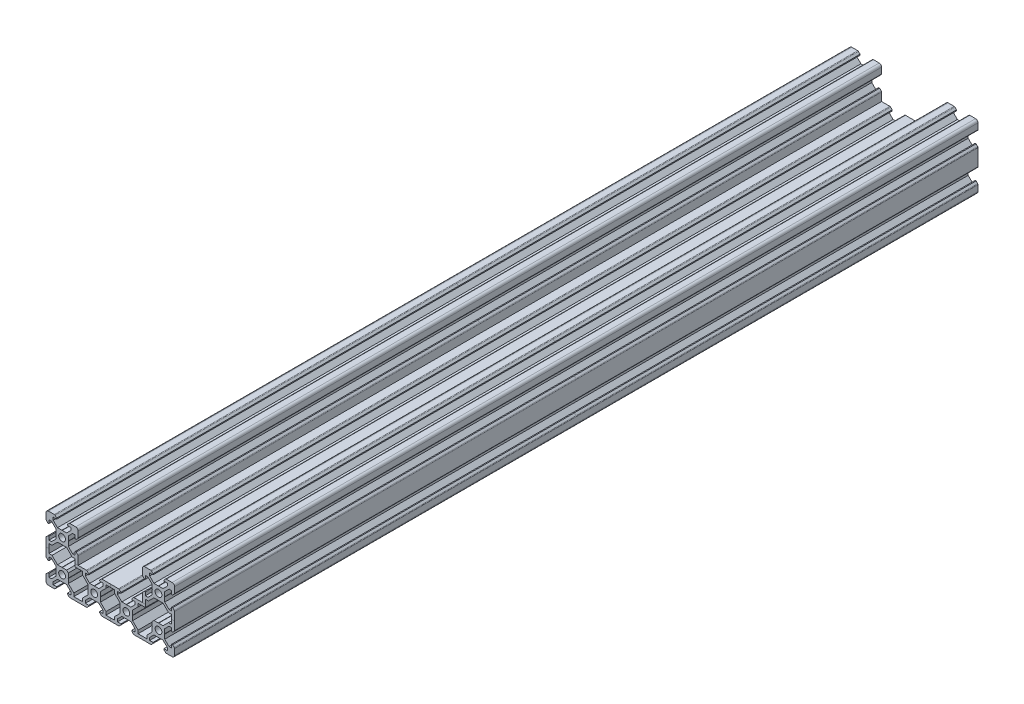
SolidWorks part; units mm, degrees
material "6063-T5"
ref_plane "Front" through (0, 0, 0) normal (0, 0, 1) x (1, 0, 0)
ref_plane "Top" through (0, 0, 0) normal (0, 1, 0) x (1, 0, 0)
ref_plane "Right" through (0, 0, 0) normal (1, 0, 0) x (0, 0, -1)
sketch "Sketch1" plane through (0, 0, 0) normal (0, 0, 1) x (1, 0, 0)
  line L0 (0, 32.3219) -> (0, -50.1713) construction
  line L1 (-2.8395, 3.9) -> (-0.1, 3.9)
  line L2 (-3.9, 2.8395) -> (-3.9, 0.1)
  line L3 (-2.8395, -3.9) -> (-0.1, -3.9)
  line L4 (3.9, 2.8395) -> (3.9, 0.1)
  line L5 (-29.7903, 0) -> (30, 0) construction
  line L6 (-0.1, -3.9) -> (0, -3.8)
  line L7 (-8.5, 10) -> (-4.8658, 10)
  line L8 (-10, 8.5) -> (-10, 4.8627)
  line L9 (-2.8395, -16.1) -> (-6.24, -12.6995)
  line L10 (10, 8.5) -> (10, 4.8627)
  line L11 (0, -3.8) -> (0.1, -3.9)
  line L12 (0.1, -3.9) -> (2.8395, -3.9)
  line L13 (-0.1, 3.9) -> (0, 3.8)
  line L14 (0, 3.8) -> (0.1, 3.9)
  line L15 (10, -10) -> (-10, 10) construction
  line L16 (-10, -10) -> (10, 10) construction
  line L17 (0.1, 3.9) -> (2.8395, 3.9)
  line L18 (-3.9, 0.1) -> (-3.8, 0)
  line L19 (-3.8, 0) -> (-3.9, -0.1)
  line L20 (-3.9, -0.1) -> (-3.9, -2.8395)
  line L21 (3.9, 0.1) -> (3.8, 0)
  line L22 (3.8, 0) -> (3.9, -0.1)
  line L23 (3.9, -0.1) -> (3.9, -2.8395)
  line L24 (0, -20) -> (58.4732, -20) construction
  line L25 (-3.9, 2.8395) -> (-6.561, 5.5005)
  line L26 (30, -50.1713) -> (30, 32.3219) construction
  line L27 (-5.5005, 8.2) -> (-3.3865, 8.2)
  line L28 (-8.2, 5.5005) -> (-8.2, 3.3865)
  line L29 (-10, -10) -> (-53.8942, -10) construction
  line L30 (8.2, 5.5005) -> (8.2, 3.3865)
  line L31 (-6.561, 5.5005) -> (-8.2, 5.5005)
  line L32 (-2.8395, 3.9) -> (-5.5005, 6.561)
  line L33 (-5.5005, 6.561) -> (-5.5005, 8.2)
  line L34 (6.561, 5.5005) -> (8.2, 5.5005)
  line L35 (3.9, 2.8395) -> (6.561, 5.5005)
  line L36 (5.5005, 6.561) -> (5.5005, 8.2)
  line L37 (2.8395, 3.9) -> (5.5005, 6.561)
  line L38 (6.561, -5.5005) -> (8.2, -5.5005)
  line L39 (-8.2, -12.6995) -> (-8.2, -7.3005)
  line L40 (2.8395, -3.9) -> (5.5005, -6.561)
  line L41 (3.9, -2.8395) -> (6.561, -5.5005)
  line L42 (-6.24, -12.6995) -> (-8.2, -12.6995)
  line L43 (-2.8395, -3.9) -> (-5.5005, -6.561)
  line L44 (-6.561, -5.5005) -> (-8.2, -5.5005)
  line L45 (-3.9, -2.8395) -> (-6.561, -5.5005)
  line L46 (30, -10) -> (10, -10) construction
  line L47 (-8.5, 10) -> (-10, 8.5) construction
  line L48 (8.5, 10) -> (10, 8.5) construction
  line L49 (-10, -10) -> (10, -30) construction
  line L50 (-5.5005, -6.561) -> (-6.24, -7.3005)
  line L51 (-3.9, -19.9) -> (-3.9, -17.1605)
  line L52 (-3.9, -17.1605) -> (-6.561, -14.4995)
  line L53 (10, 32.3219) -> (10, -50.1713) construction
  line L54 (-10, -30) -> (10, -10) construction
  line L55 (-4.3771, 9.7976) -> (-3.3865, 8.807)
  line L56 (-3.3865, 8.807) -> (-3.3865, 8.2)
  line L57 (4.3771, 9.7976) -> (3.3865, 8.807)
  line L58 (3.3865, 8.807) -> (3.3865, 8.2)
  line L59 (4.8658, 10) -> (8.5, 10)
  line L60 (3.3865, 8.2) -> (5.5005, 8.2)
  line L61 (-9.7968, 4.3732) -> (-8.807, 3.3865)
  line L62 (-8.807, 3.3865) -> (-8.2, 3.3865)
  line L63 (-9.7976, -4.3802) -> (-8.807, -3.3865)
  line L64 (-8.807, -3.3865) -> (-8.2, -3.3865)
  line L65 (9.7968, 4.3732) -> (8.807, 3.3865)
  line L66 (8.807, 3.3865) -> (8.2, 3.3865)
  line L67 (8.807, -3.3865) -> (8.2, -3.3865)
  line L68 (9.7976, -4.3802) -> (8.807, -3.3865)
  line L69 (-10, -4.87) -> (-10, -15.13)
  line L70 (-8.2, -3.3865) -> (-8.2, -5.5005)
  line L71 (10, -4.87) -> (10, -10)
  line L72 (8.2, -3.3865) -> (8.2, -5.5005)
  line L73 (-6.561, -14.4995) -> (-8.2, -14.4995)
  line L74 (-8.2, -16.6135) -> (-8.2, -14.4995)
  line L75 (-8.807, -16.6135) -> (-8.2, -16.6135)
  line L76 (-9.7976, -15.6198) -> (-8.807, -16.6135)
  line L77 (-10, -28.5) -> (-10, -24.8627)
  line L78 (-9.7968, -24.3732) -> (-8.807, -23.3865)
  line L79 (-8.807, -23.3865) -> (-8.2, -23.3865)
  line L80 (-8.2, -25.5005) -> (-8.2, -23.3865)
  line L81 (-6.561, -25.5005) -> (-8.2, -25.5005)
  line L82 (-3.9, -22.8395) -> (-6.561, -25.5005)
  line L83 (-3.9, -22.8395) -> (-3.9, -20.1)
  line L84 (-3.9, -20.1) -> (-3.8, -20)
  line L85 (-3.8, -20) -> (-3.9, -19.9)
  line L86 (0, -23.8) -> (0.1, -23.9)
  line L87 (-0.1, -23.9) -> (0, -23.8)
  line L88 (-2.8395, -23.9) -> (-0.1, -23.9)
  line L89 (0.1, -23.9) -> (2.8395, -23.9)
  line L90 (-2.8395, -23.9) -> (-5.5005, -26.561)
  line L91 (-5.5005, -28.2) -> (-3.3865, -28.2)
  line L92 (-5.5005, -26.561) -> (-5.5005, -28.2)
  line L93 (-4.3771, -29.7976) -> (-3.3865, -28.807)
  line L94 (-3.3865, -28.807) -> (-3.3865, -28.2)
  line L95 (-4.8658, -30) -> (-8.5, -30)
  line L96 (5.5005, -26.561) -> (5.5005, -28.2)
  line L97 (2.8395, -23.9) -> (5.5005, -26.561)
  line L98 (4.3771, -29.7976) -> (3.3865, -28.807)
  line L99 (3.3865, -28.807) -> (3.3865, -28.2)
  line L100 (3.3865, -28.2) -> (5.5005, -28.2)
  line L101 (4.8658, -30) -> (10, -30)
  line L102 (0.1, -16.1) -> (2.8395, -16.1)
  line L103 (0, -16.2) -> (0.1, -16.1)
  line L104 (-0.1, -16.1) -> (0, -16.2)
  line L105 (-2.8395, -16.1) -> (-0.1, -16.1)
  line L106 (3.9, -22.8395) -> (3.9, -20.1)
  line L107 (3.9, -20.1) -> (3.8, -20)
  line L108 (3.8, -20) -> (3.9, -19.9)
  line L109 (3.9, -19.9) -> (3.9, -17.1605)
  line L110 (3.9, -17.1605) -> (2.8395, -16.1)
  line L111 (-6.24, -7.3005) -> (-8.2, -7.3005)
  line L112 (6.24, -7.3005) -> (8.2, -7.3005)
  line L113 (5.5005, -6.561) -> (6.24, -7.3005)
  line L114 (12.6995, -28.2) -> (7.3005, -28.2)
  line L115 (7.3005, -28.2) -> (7.3005, -26.24)
  line L116 (7.3005, -26.24) -> (3.9, -22.8395)
  line L117 (16.1, -19.9) -> (16.1, -17.1605)
  line L118 (16.2, -20) -> (16.1, -19.9)
  line L119 (16.1, -20.1) -> (16.2, -20)
  line L120 (16.1, -22.8395) -> (16.1, -20.1)
  line L121 (20, -16.2) -> (19.9, -16.1)
  line L122 (20.1, -16.1) -> (20, -16.2)
  line L123 (22.8395, -16.1) -> (20.1, -16.1)
  line L124 (19.9, -16.1) -> (17.1605, -16.1)
  line L125 (23.9, -19.9) -> (23.9, -17.1605)
  line L126 (23.8, -20) -> (23.9, -19.9)
  line L127 (23.9, -20.1) -> (23.8, -20)
  line L128 (23.9, -22.8395) -> (23.9, -20.1)
  line L129 (20.1, -23.9) -> (20, -23.8)
  line L130 (22.8395, -23.9) -> (20.1, -23.9)
  line L131 (20, -23.8) -> (19.9, -23.9)
  line L132 (19.9, -23.9) -> (17.1605, -23.9)
  line L133 (12.6995, -28.2) -> (12.6995, -26.24)
  line L134 (14.4995, -26.561) -> (14.4995, -28.2)
  line L135 (17.1605, -23.9) -> (14.4995, -26.561)
  line L136 (12.6995, -26.24) -> (16.1, -22.8395)
  line L137 (16.6135, -28.807) -> (16.6135, -28.2)
  line L138 (16.6135, -28.2) -> (14.4995, -28.2)
  line L139 (15.6229, -29.7976) -> (16.6135, -28.807)
  line L140 (15.1342, -30) -> (10, -30)
  line L141 (20, 32.3219) -> (20, -50.1713) construction
  line L142 (10, -10) -> (30, -30) construction
  line L143 (30, -10) -> (10, -30) construction
  line L144 (27.3005, -28.2) -> (27.3005, -26.24)
  line L145 (25.5005, -26.561) -> (25.5005, -28.2)
  line L146 (24.3771, -29.7976) -> (23.3865, -28.807)
  line L147 (23.3865, -28.807) -> (23.3865, -28.2)
  line L148 (23.3865, -28.2) -> (25.5005, -28.2)
  line L149 (24.8658, -30) -> (30, -30)
  line L150 (27.3005, -28.2) -> (32.6995, -28.2)
  line L151 (25.5005, -26.561) -> (22.8395, -23.9)
  line L152 (27.3005, -26.24) -> (23.9, -22.8395)
  line L153 (25.5005, -13.439) -> (25.5005, -11.8)
  line L154 (27.3005, -11.8) -> (27.3005, -13.76)
  line L155 (27.3005, -13.76) -> (23.9, -17.1605)
  line L156 (25.5005, -13.439) -> (22.8395, -16.1)
  line L157 (12.6995, -11.8) -> (12.6995, -13.76)
  line L158 (14.4995, -13.439) -> (14.4995, -11.8)
  line L159 (17.1605, -16.1) -> (14.4995, -13.439)
  line L160 (16.1, -17.1605) -> (12.6995, -13.76)
  line L161 (23.3865, -11.193) -> (23.3865, -11.8)
  line L162 (16.6135, -11.193) -> (16.6135, -11.8)
  line L163 (16.6135, -11.8) -> (14.4995, -11.8)
  line L164 (23.3865, -11.8) -> (25.5005, -11.8)
  line L165 (15.6229, -10.2024) -> (16.6135, -11.193)
  line L166 (24.3771, -10.2024) -> (23.3865, -11.193)
  line L167 (24.8658, -10) -> (30, -10)
  line L168 (27.3005, -11.8) -> (32.6995, -11.8)
  line L169 (15.1342, -10) -> (10, -10)
  line L170 (12.6995, -11.8) -> (8.2, -11.8)
  line L171 (8.2, -11.8) -> (8.2, -7.3005)
  line L172 (60, -3.8) -> (59.9, -3.9)
  line L173 (60.1, -3.9) -> (60, -3.8)
  line L174 (63.8, 0) -> (63.9, -0.1)
  line L175 (63.9, 0.1) -> (63.8, 0)
  line L176 (56.1, 0.1) -> (56.2, 0)
  line L177 (56.2, 0) -> (56.1, -0.1)
  line L178 (60.1, 3.9) -> (60, 3.8)
  line L179 (60, 3.8) -> (59.9, 3.9)
  line L180 (62.8395, 3.9) -> (60.1, 3.9)
  line L181 (59.9, 3.9) -> (57.1605, 3.9)
  line L182 (63.9, 2.8395) -> (63.9, 0.1)
  line L183 (63.9, -0.1) -> (63.9, -2.8395)
  line L184 (62.8395, -3.9) -> (60.1, -3.9)
  line L185 (59.9, -3.9) -> (57.1605, -3.9)
  line L186 (56.1, -0.1) -> (56.1, -2.8395)
  line L187 (56.1, 2.8395) -> (56.1, 0.1)
  line L188 (60, -23.8) -> (59.9, -23.9)
  line L189 (60.1, -23.9) -> (60, -23.8)
  line L190 (60, -16.2) -> (59.9, -16.1)
  line L191 (60.1, -16.1) -> (60, -16.2)
  line L192 (63.8, -20) -> (63.9, -19.9)
  line L193 (63.9, -20.1) -> (63.8, -20)
  line L194 (56.2, -20) -> (56.1, -19.9)
  line L195 (56.1, -20.1) -> (56.2, -20)
  line L196 (40, -16.2) -> (40.1, -16.1)
  line L197 (39.9, -16.1) -> (40, -16.2)
  line L198 (36.2, -20) -> (36.1, -19.9)
  line L199 (36.1, -20.1) -> (36.2, -20)
  line L200 (43.8, -20) -> (43.9, -19.9)
  line L201 (43.9, -20.1) -> (43.8, -20)
  line L202 (40, -23.8) -> (40.1, -23.9)
  line L203 (39.9, -23.9) -> (40, -23.8)
  line L204 (56.1, -22.8395) -> (56.1, -20.1)
  line L205 (59.9, -23.9) -> (57.1605, -23.9)
  line L206 (62.8395, -23.9) -> (60.1, -23.9)
  line L207 (63.9, -22.8395) -> (63.9, -20.1)
  line L208 (63.9, -19.9) -> (63.9, -17.1605)
  line L209 (62.8395, -16.1) -> (60.1, -16.1)
  line L210 (59.9, -16.1) -> (57.1605, -16.1)
  line L211 (56.1, -19.9) -> (56.1, -17.1605)
  line L212 (43.9, -19.9) -> (43.9, -17.1605)
  line L213 (43.9, -22.8395) -> (43.9, -20.1)
  line L214 (40.1, -23.9) -> (42.8395, -23.9)
  line L215 (37.1605, -23.9) -> (39.9, -23.9)
  line L216 (36.1, -22.8395) -> (36.1, -20.1)
  line L217 (36.1, -19.9) -> (36.1, -17.1605)
  line L218 (37.1605, -16.1) -> (39.9, -16.1)
  line L219 (40.1, -16.1) -> (42.8395, -16.1)
  line L220 (42.8395, -23.9) -> (45.5005, -26.561)
  line L221 (47.3005, -26.24) -> (43.9, -22.8395)
  line L222 (43.9, -17.1605) -> (47.3005, -13.76)
  line L223 (42.8395, -16.1) -> (45.5005, -13.439)
  line L224 (34.4995, -13.439) -> (37.1605, -16.1)
  line L225 (32.6995, -13.76) -> (36.1, -17.1605)
  line L226 (34.4995, -26.561) -> (37.1605, -23.9)
  line L227 (32.6995, -26.24) -> (36.1, -22.8395)
  line L228 (47.3005, -11.8) -> (47.3005, -13.76)
  line L229 (45.5005, -13.439) -> (45.5005, -11.8)
  line L230 (47.3005, -28.2) -> (47.3005, -26.24)
  line L231 (45.5005, -26.561) -> (45.5005, -28.2)
  line L232 (34.4995, -26.561) -> (34.4995, -28.2)
  line L233 (32.6995, -28.2) -> (32.6995, -26.24)
  line L234 (34.4995, -13.439) -> (34.4995, -11.8)
  line L235 (32.6995, -11.8) -> (32.6995, -13.76)
  line L236 (43.3865, -28.2) -> (45.5005, -28.2)
  line L237 (43.3865, -28.807) -> (43.3865, -28.2)
  line L238 (44.3771, -29.7976) -> (43.3865, -28.807)
  line L239 (35.6229, -29.7976) -> (36.6135, -28.807)
  line L240 (36.6135, -28.807) -> (36.6135, -28.2)
  line L241 (36.6135, -28.2) -> (34.4995, -28.2)
  line L242 (44.3771, -10.2024) -> (43.3865, -11.193)
  line L243 (43.3865, -11.193) -> (43.3865, -11.8)
  line L244 (43.3865, -11.8) -> (45.5005, -11.8)
  line L245 (35.6229, -10.2024) -> (36.6135, -11.193)
  line L246 (36.6135, -11.193) -> (36.6135, -11.8)
  line L247 (36.6135, -11.8) -> (34.4995, -11.8)
  line L248 (35.1342, -30) -> (30, -30)
  line L249 (35.1342, -10) -> (30, -10)
  line L250 (51.8, -3.3865) -> (51.8, -5.5005)
  line L251 (51.193, -3.3865) -> (51.8, -3.3865)
  line L252 (50.2024, -4.3802) -> (51.193, -3.3865)
  line L253 (51.8, -11.8) -> (51.8, -7.3005)
  line L254 (50, -4.87) -> (50, -10)
  line L255 (44.8658, -10) -> (50, -10)
  line L256 (47.3005, -11.8) -> (51.8, -11.8)
  line L257 (62.8395, -16.1) -> (66.24, -12.6995)
  line L258 (63.9, -17.1605) -> (66.561, -14.4995)
  line L259 (63.9, -22.8395) -> (66.561, -25.5005)
  line L260 (62.8395, -23.9) -> (65.5005, -26.561)
  line L261 (57.1605, -23.9) -> (54.4995, -26.561)
  line L262 (52.6995, -26.24) -> (56.1, -22.8395)
  line L263 (63.9, 2.8395) -> (66.561, 5.5005)
  line L264 (62.8395, 3.9) -> (65.5005, 6.561)
  line L265 (57.1605, 3.9) -> (54.4995, 6.561)
  line L266 (56.1, 2.8395) -> (53.439, 5.5005)
  line L267 (63.9, -2.8395) -> (66.561, -5.5005)
  line L268 (62.8395, -3.9) -> (65.5005, -6.561)
  line L269 (57.1605, -3.9) -> (54.4995, -6.561)
  line L270 (56.1, -2.8395) -> (53.439, -5.5005)
  line L271 (64.3771, -29.7976) -> (63.3865, -28.807)
  line L272 (64.8658, -30) -> (68.5, -30)
  line L273 (65.5005, -28.2) -> (63.3865, -28.2)
  line L274 (55.6229, -29.7976) -> (56.6135, -28.807)
  line L275 (56.6135, -28.2) -> (54.4995, -28.2)
  line L276 (56.6135, -28.807) -> (56.6135, -28.2)
  line L277 (55.1342, -30) -> (50, -30)
  line L278 (44.8658, -30) -> (50, -30)
  line L279 (44.3771, -29.7976) -> (43.3865, -28.807)
  line L280 (43.3865, -28.807) -> (43.3865, -28.2)
  line L281 (43.3865, -28.2) -> (45.5005, -28.2)
  line L282 (47.3005, -28.2) -> (52.6995, -28.2)
  line L283 (70, -28.5) -> (70, -24.8627)
  line L284 (65.5005, -26.561) -> (65.5005, -28.2)
  line L285 (54.4995, -26.561) -> (54.4995, -28.2)
  line L286 (52.6995, -28.2) -> (52.6995, -26.24)
  line L287 (47.3005, -28.2) -> (47.3005, -26.24)
  line L288 (45.5005, -26.561) -> (45.5005, -28.2)
  line L289 (66.561, -5.5005) -> (68.2, -5.5005)
  line L290 (66.24, -7.3005) -> (68.2, -7.3005)
  line L291 (69.7976, -4.3802) -> (68.807, -3.3865)
  line L292 (68.807, -3.3865) -> (68.2, -3.3865)
  line L293 (68.2, -3.3865) -> (68.2, -5.5005)
  line L294 (68.2, -12.6995) -> (68.2, -7.3005)
  line L295 (70, -4.87) -> (70, -15.13)
  line L296 (69.7976, -15.6198) -> (68.807, -16.6135)
  line L297 (68.807, -16.6135) -> (68.2, -16.6135)
  line L298 (68.2, -16.6135) -> (68.2, -14.4995)
  line L299 (66.561, -14.4995) -> (68.2, -14.4995)
  line L300 (66.24, -12.6995) -> (68.2, -12.6995)
  line L301 (56.1, -17.1605) -> (57.1605, -16.1)
  line L302 (66.561, -25.5005) -> (68.2, -25.5005)
  line L303 (68.2, -25.5005) -> (68.2, -23.3865)
  line L304 (68.807, -23.3865) -> (68.2, -23.3865)
  line L305 (69.7968, -24.3732) -> (68.807, -23.3865)
  line L306 (53.76, -7.3005) -> (51.8, -7.3005)
  line L307 (53.439, -5.5005) -> (51.8, -5.5005)
  line L308 (54.4995, -6.561) -> (53.76, -7.3005)
  line L309 (65.5005, -6.561) -> (66.24, -7.3005)
  line L310 (54.4995, 6.561) -> (54.4995, 8.2)
  line L311 (56.6135, 8.2) -> (54.4995, 8.2)
  line L312 (56.6135, 8.807) -> (56.6135, 8.2)
  line L313 (55.6229, 9.7976) -> (56.6135, 8.807)
  line L314 (55.1342, 10) -> (51.5, 10)
  line L315 (50, 8.5) -> (50, 4.8627)
  line L316 (50.2032, 4.3732) -> (51.193, 3.3865)
  line L317 (51.193, 3.3865) -> (51.8, 3.3865)
  line L318 (51.8, 5.5005) -> (51.8, 3.3865)
  line L319 (53.439, 5.5005) -> (51.8, 5.5005)
  line L320 (66.561, 5.5005) -> (68.2, 5.5005)
  line L321 (68.2, 5.5005) -> (68.2, 3.3865)
  line L322 (68.807, 3.3865) -> (68.2, 3.3865)
  line L323 (69.7968, 4.3732) -> (68.807, 3.3865)
  line L324 (70, 8.5) -> (70, 4.8627)
  line L325 (68.5, 10) -> (64.8658, 10)
  line L326 (64.3771, 9.7976) -> (63.3865, 8.807)
  line L327 (63.3865, 8.807) -> (63.3865, 8.2)
  line L328 (65.5005, 8.2) -> (63.3865, 8.2)
  line L329 (65.5005, 6.561) -> (65.5005, 8.2)
  line L330 (63.3865, -28.807) -> (63.3865, -28.2)
  circle A0 centre (0, 0) radius 2.1
  circle A1 centre (0, -20) radius 2.1
  circle A2 centre (20, -20) radius 2.1
  circle A3 centre (60, 0) radius 2.1
  circle A4 centre (60, -20) radius 2.1
  circle A5 centre (40, -20) radius 2.1
  arc A6 (-8.5, 10) -> (-10, 8.5) centre (-8.5, 8.5) ccw
  arc A7 (10, 8.5) -> (8.5, 10) centre (8.5, 8.5) ccw
  arc A8 (-4.3771, 9.7976) -> (-4.8658, 10) centre (-4.8658, 9.3088) ccw
  arc A9 (4.3771, 9.7976) -> (4.8658, 10) centre (4.8658, 9.3088) cw
  arc A10 (-10, 4.8627) -> (-9.7968, 4.3732) centre (-9.3088, 4.8627) ccw
  arc A11 (9.7968, 4.3732) -> (10, 4.8627) centre (9.3088, 4.8627) ccw
  arc A12 (10, -4.87) -> (9.7976, -4.3802) centre (9.3062, -4.87) ccw
  arc A13 (-9.7976, -4.3802) -> (-10, -4.87) centre (-9.3062, -4.87) ccw
  arc A14 (-9.7976, -15.6198) -> (-10, -15.13) centre (-9.3062, -15.13) cw
  arc A15 (-8.5, -30) -> (-10, -28.5) centre (-8.5, -28.5) cw
  arc A16 (-10, -24.8627) -> (-9.7968, -24.3732) centre (-9.3088, -24.8627) cw
  arc A17 (-4.3771, -29.7976) -> (-4.8658, -30) centre (-4.8658, -29.3088) cw
  arc A18 (4.3771, -29.7976) -> (4.8658, -30) centre (4.8658, -29.3088) ccw
  arc A19 (15.6229, -29.7976) -> (15.1342, -30) centre (15.1342, -29.3088) cw
  arc A20 (24.3771, -29.7976) -> (24.8658, -30) centre (24.8658, -29.3088) ccw
  arc A21 (15.6229, -10.2024) -> (15.1342, -10) centre (15.1342, -10.6912) ccw
  arc A22 (24.3771, -10.2024) -> (24.8658, -10) centre (24.8658, -10.6912) cw
  arc A23 (44.3771, -29.7976) -> (44.8658, -30) centre (44.8658, -29.3088) ccw
  arc A24 (35.6229, -29.7976) -> (35.1342, -30) centre (35.1342, -29.3088) cw
  arc A25 (44.3771, -10.2024) -> (44.8658, -10) centre (44.8658, -10.6912) cw
  arc A26 (35.6229, -10.2024) -> (35.1342, -10) centre (35.1342, -10.6912) ccw
  arc A27 (50, -4.87) -> (50.2024, -4.3802) centre (50.6938, -4.87) cw
  arc A28 (64.3771, -29.7976) -> (64.8658, -30) centre (64.8658, -29.3088) ccw
  arc A29 (68.5, -30) -> (70, -28.5) centre (68.5, -28.5) ccw
  arc A30 (55.6229, -29.7976) -> (55.1342, -30) centre (55.1342, -29.3088) cw
  arc A31 (44.3771, -29.7976) -> (44.8658, -30) centre (44.8658, -29.3088) ccw
  arc A32 (69.7976, -4.3802) -> (70, -4.87) centre (69.3062, -4.87) cw
  arc A33 (69.7976, -15.6198) -> (70, -15.13) centre (69.3062, -15.13) ccw
  arc A34 (70, -24.8627) -> (69.7968, -24.3732) centre (69.3088, -24.8627) ccw
  arc A35 (55.6229, 9.7976) -> (55.1342, 10) centre (55.1342, 9.3088) ccw
  arc A36 (50, 8.5) -> (51.5, 10) centre (51.5, 8.5) cw
  arc A37 (50.2032, 4.3732) -> (50, 4.8627) centre (50.6912, 4.8627) cw
  arc A38 (70, 4.8627) -> (69.7968, 4.3732) centre (69.3088, 4.8627) cw
  arc A39 (68.5, 10) -> (70, 8.5) centre (68.5, 8.5) cw
  arc A40 (64.3771, 9.7976) -> (64.8658, 10) centre (64.8658, 9.3088) cw
  point P23 (-9.25, 9.25)
  point P69 (9.25, 9.25)
  point P188 (10, -28.2)
  point P223 (30, -28.2)
  point P320 (30, -11.8)
  dimension "D1" = 4.2
  dimension "D16" = 1.5
  dimension "D21" = 0.529
  dimension "D25" = 0.53
  dimension "D27" = 90
  dimension "D2" = 0.1
  dimension "D3" = 0.1
  dimension "D4" = 7.8
  dimension "D5" = 7.8
  dimension "D6" = 20
  dimension "D7" = 20
  dimension "D8" = 20
  dimension "D9" = 10
  dimension "D10" = 0.1
  dimension "D11" = 1.8
  dimension "D12" = 1.8
  dimension "D13" = 5.679
  dimension "D14" = 5.679
  dimension "D15" = 1.639
  dimension "D17" = 90
  dimension "D18" = 6.773
  dimension "D19" = 0.607
  dimension "D20" = 11.001
  dimension "D22" = 0.607
  dimension "D23" = 90
  dimension "D24" = 6.773
  dimension "D26" = 0.53
  dimension "D28" = 0.53
  dimension "D29" = 0.53
  dimension "D30" = 1.8
extrude "Boss-Extrude1" add sketch "Sketch1" along normal blind 500 contours A40 L326 L327 L328 L329 L264 L180 L178 L179 L181 L265 L310 L311 L312 L313 A35 L314 A36 L315 A37 L316 L317 L318 L319 L266 L187 L176 L177 L186 L270 L307 L250 L251 L252 A27 L254 L255 A25 L242 L243 L244 L229 L223 L219 L196 L197 L218 L224 L234 L247 L246
sketch "Sketch2" plane through (0, 0, 500) normal (0, 0, 1) x (1, 0, 0)
  line L0 (-10, -10) -> (70, -10)
  line L1 (-10, -4.87) -> (-10, -15.13) construction
  line L2 (70, -4.87) -> (70, -15.13) construction
split line "TopFixture1 - SplitLine"
sketch "Sketch3" plane through (0, 0, 0) normal (0, 0, -1) x (-1, 0, 0)
  line L0 (-70, -10) -> (10, -10)
  line L1 (-70, -4.87) -> (-70, -15.13) construction
  line L2 (10, -4.87) -> (10, -15.13) construction
split line "TopFixture2 - SplitLine"
sketch "Sketch6" plane through (0, 10, 0) normal (0, 1, 0) x (1, 0, 0)
  line L0 (-8.5, -250) -> (68.5, -250)
  line L1 (-8.5, -500) -> (-8.5, 0) construction
  line L2 (68.5, -500) -> (68.5, 0) construction
split line "TopFixture3 - SplitLine"
sketch "Sketch7" plane through (0, 0, 500) normal (0, 0, 1) x (1, 0, 0)
  line L0 (30, -30) -> (30, -10)
  line L1 (24.8658, -30) -> (35.1342, -30) construction
  line L2 (35.1342, -10) -> (24.8658, -10) construction
split line "SideFixture1 - SplitLine"
sketch "Sketch8" plane through (0, 0, 0) normal (0, 0, -1) x (-1, 0, 0)
  line L0 (-30, -10) -> (-30, -30)
  line L1 (-35.1342, -10) -> (-24.8658, -10) construction
  line L2 (-24.8658, -30) -> (-35.1342, -30) construction
split line "SideFixture2 - SplitLine"
sketch "Sketch9" plane through (-10, 0, 0) normal (-1, 0, 0) x (0, 0, 1)
  line L0 (250, -28.5) -> (250, 8.5)
  line L3 (500, -28.5) -> (0, -28.5) construction
  line L4 (500, 8.5) -> (0, 8.5) construction
split line "SideFixture3 - SplitLine"
